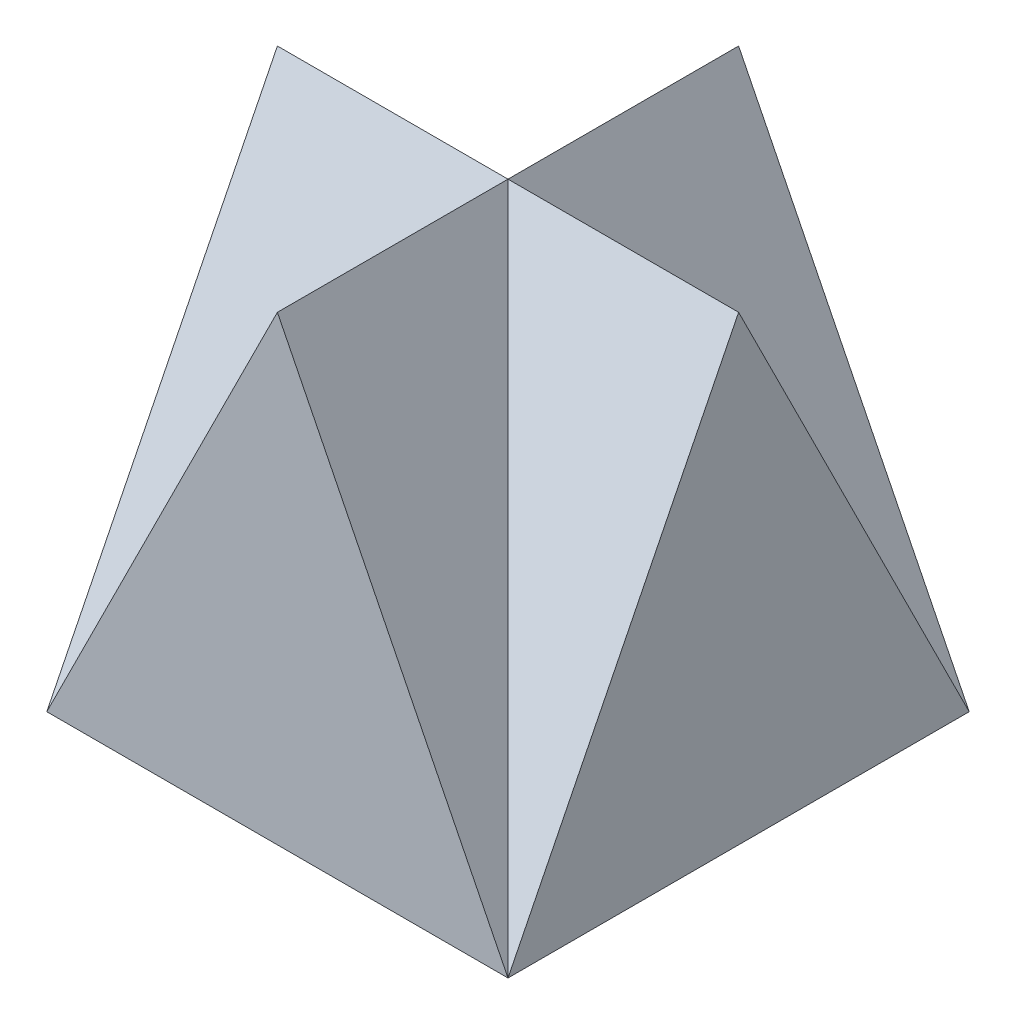
SolidWorks part; units mm, degrees
ref_plane "Front" through (0, 0, 0) normal (0, 0, 1) x (1, 0, 0)
ref_plane "Top" through (0, 0, 0) normal (0, 1, 0) x (1, 0, 0)
ref_plane "Right" through (0, 0, 0) normal (1, 0, 0) x (0, 0, -1)
sketch "Sketch1" plane through (0, 0, 0) normal (0, 1, 0) x (1, 0, 0)
  line L1 (-2, -2) -> (2, -2)
  line L2 (-2, -2) -> (-2, 2)
  line L3 (-2, 2) -> (2, 2)
  line L4 (2, -2) -> (2, 2)
  line L5 (-2, -2) -> (2, 2) construction
  line L6 (-2, 2) -> (2, -2) construction
  point P0 (0, 0)
  dimension "D1" = 4
  dimension "D2" = 4
extrude "Boss-Extrude1" add sketch "Sketch1" along normal blind 4
sketch3d "3DSketch3"
  line L2 (2, 4, -2) -> (-2, 4, -2) construction
  line L6 (0, 4, 0) -> (0, 4, 2)
  line L7 (-2, 4, 2) -> (2, 4, 2) construction
  line L8 (0, 4, 2) -> (-2, 0, 2)
  line L9 (-2, 0, 2) -> (0, 4, 0)
  point P5 (0, 4, 0)
  dimension "D1" = 2
  dimension "D2" = 2
extrude "Cut-Extrude5" cut sketch "3DSketch3" along direction (1, 0, 0) on the side of the normal blind 32 contours L9 L6 L8
sketch3d "3DSketch4"
  line L4 (0, 4, 0) -> (-2, 4, 0)
  line L5 (-2, 4, 0) -> (-2, 0, -2)
  line L6 (-2, 0, -2) -> (0, 4, 0)
extrude "Cut-Extrude6" cut sketch "3DSketch4" along direction (0, -1, 0) on the side of the normal blind 32
sketch3d "3DSketch5"
  line L1 (0, 4, 0) -> (-2, 0, -2)
  line L2 (0, 4, 0) -> (0, 4, -2)
  line L3 (2, 4, -2) -> (-2, 4, -2) construction
  line L5 (-2, 0, -2) -> (0, 4, -2)
extrude "Cut-Extrude7" cut sketch "3DSketch5" along direction (-1, 0, 0) on the side against the normal blind 32
sketch3d "3DSketch6"
  line L0 (2, 0, 2) -> (0, 4, 0)
  line L1 (0, 4, 0) -> (0, 4, 2)
  line L2 (0, 4, 2) -> (2, 0, 2)
  line L3 (0, 4, 0) -> (0, 4, -2)
  line L4 (0, 4, -2) -> (2, 0, -2)
  line L5 (2, 0, -2) -> (0, 4, 0)
extrude "Cut-Extrude8" cut sketch "3DSketch6" along direction (-1, 0, 0) on the side of the normal blind 32 contours L1 L2 L0 | L5 L3 L4
